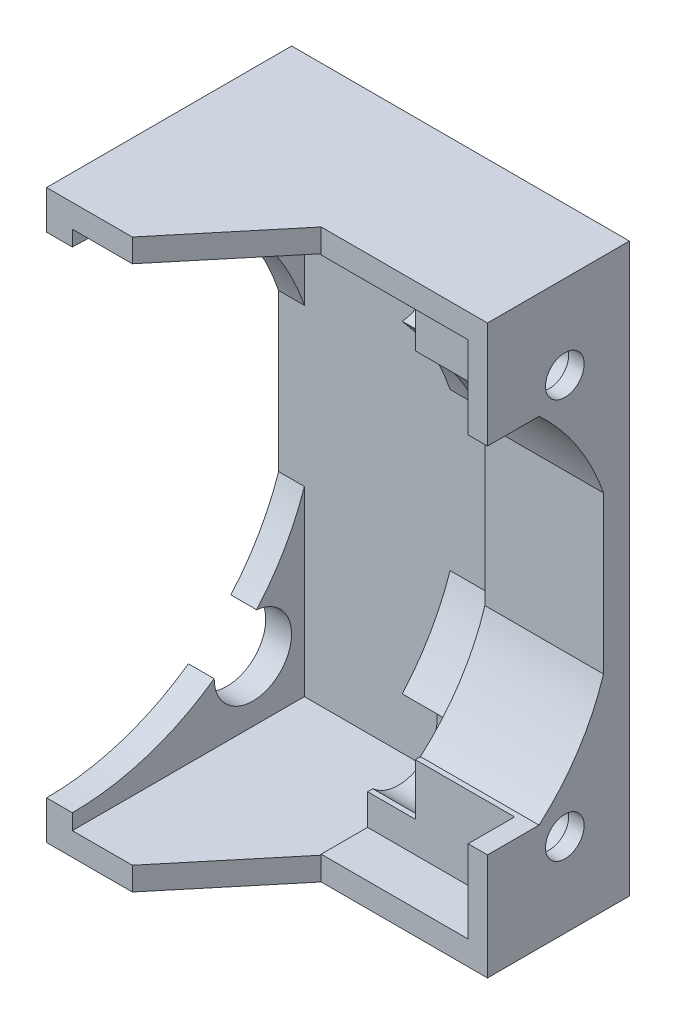
SolidWorks part; units mm, degrees
ref_plane "Alzado" through (0, 0, 0) normal (0, 0, 1) x (1, 0, 0)
ref_plane "Planta" through (0, 0, 0) normal (0, 1, 0) x (1, 0, 0)
ref_plane "Vista lateral" through (0, 0, 0) normal (1, 0, 0) x (0, 0, -1)
sketch "Croquis1" plane through (0, 0, 0) normal (0, 0, 1) x (1, 0, 0)
  line L1 (-34.6141, 8.9096) -> (-9.6141, 8.9096)
  line L2 (-34.6141, 8.9096) -> (-34.6141, -35.0904)
  line L3 (-34.6141, -35.0904) -> (-9.6141, -35.0904)
  line L4 (-9.6141, 8.9096) -> (-9.6141, -35.0904)
  dimension "D1" = 25
  dimension "D2" = 44
extrude "Saliente-Extruir1" add sketch "Croquis1" along normal blind 20
sketch "Croquis2" plane through (0, 0, 20) normal (0, 0, 1) x (1, 0, 0)
  line L0 (-34.6141, 8.9096) -> (-34.6141, -35.0904) construction
  line L1 (-32.6141, 7.1096) -> (-21.3141, 7.1096)
  line L2 (-32.6141, 7.1096) -> (-32.6141, -33.2904)
  line L3 (-32.6141, -33.2904) -> (-21.3141, -33.2904)
  line L4 (-21.3141, 7.1096) -> (-21.3141, -33.2904)
  line L5 (-9.6141, 8.9096) -> (-34.6141, 8.9096) construction
  dimension "D1" = 2
  dimension "D2" = 11.3
  dimension "D3" = 1.8
  dimension "D4" = 40.4
extrude "Cortar-Extruir1" cut sketch "Croquis2" against normal blind 18
sketch "Croquis3" plane through (0, 0, 20) normal (0, 0, 1) x (1, 0, 0)
  line L0 (-34.6141, -35.0904) -> (-9.6141, -35.0904) construction
  line L1 (-9.6141, 8.9096) -> (-20.3141, 8.9096)
  line L2 (-9.6141, 8.9096) -> (-9.6141, -35.0904)
  line L3 (-9.6141, -35.0904) -> (-20.3141, -35.0904)
  line L4 (-20.3141, 8.9096) -> (-20.3141, -35.0904)
  line L5 (-21.3141, -33.2904) -> (-21.3141, 7.1096) construction
  dimension "D1" = 1
extrude "Cortar-Extruir2" cut sketch "Croquis3" against normal blind 12
sketch "Croquis4" plane through (-34.6141, 0, 0) normal (-1, 0, 0) x (0, 0, 1)
  line L1 (20, 5.9096) -> (20, -32.0904)
  line L2 (0, 8.9096) -> (0, -35.0904) construction
  line L5 (20, 8.9096) -> (0, 8.9096) construction
  circle A0 centre (6, 2.4096) radius 1.6
  arc A1 (20, 5.9096) -> (20, -32.0904) centre (20, -13.0904) ccw
  circle A2 centre (6, -28.5904) radius 1.6
  dimension "D1" = 6
  dimension "D3" = 31
  dimension "D2" = 6.5
  dimension "D4" = 6
extrude "Cortar-Extruir3" cut sketch "Croquis4" against normal up to vertex
sketch "Croquis5" plane through (-34.6141, 0, 0) normal (-1, 0, 0) x (0, 0, 1)
  circle A0 centre (6, 2.4096) radius 3
  circle A1 centre (6, -28.5904) radius 3
extrude "Cortar-Extruir4" cut sketch "Croquis5" against normal blind 17
sketch "Croquis7" plane through (0, 0, 8) normal (0, 0, 1) x (1, 0, 0)
  line L0 (-20.3141, -30.8265) -> (-20.3141, -35.0904) construction
  line L1 (-9.6141, -35.0904) -> (-20.3141, -35.0904)
  line L2 (-9.6141, -35.0904) -> (-9.6141, -32.9585)
  line L3 (-9.6141, -32.9585) -> (-20.3141, -32.9585)
  line L4 (-20.3141, -35.0904) -> (-20.3141, -32.9585)
  line L5 (-20.3141, 8.9096) -> (-20.3141, 4.6456) construction
  line L6 (-9.6141, 8.9096) -> (-20.3141, 8.9096)
  line L7 (-9.6141, 8.9096) -> (-9.6141, 6.7776)
  line L8 (-9.6141, 6.7776) -> (-20.3141, 6.7776)
  line L9 (-20.3141, 8.9096) -> (-20.3141, 6.7776)
extrude "Saliente-Extruir2" add sketch "Croquis7" along normal up to vertex (12 mm away)
sketch "Croquis9" plane through (0, 0, 2) normal (0, 0, 1) x (1, 0, 0)
  line L1 (-21.3141, -7.0077) -> (-32.6141, -7.0077)
  line L2 (-21.3141, -7.0077) -> (-21.3141, -19.1732)
  line L3 (-21.3141, -19.1732) -> (-32.6141, -19.1732)
  line L4 (-32.6141, -7.0077) -> (-32.6141, -19.1732)
extrude "Saliente-Extruir3" add sketch "Croquis9" against normal up to vertex (2 mm away)
sketch "Croquis11" plane through (-32.6141, 0, 0) normal (-1, 0, 0) x (0, 0, 1)
  line L0 (2, -7.0077) -> (2, -19.1732)
  arc A0 (2, -7.0077) -> (2, -19.1732) centre (20, -13.0904) ccw
extrude "Saliente-Extruir4" add sketch "Croquis11" along normal up to vertex (2 mm away)
sketch "Croquis12" plane through (-34.6141, 0, 0) normal (-1, 0, 0) x (0, 0, 1)
  line L0 (20, -35.0904) -> (0, -35.0904) construction
  line L1 (0, 8.9096) -> (0.99, 8.9096)
  line L2 (0, 8.9096) -> (0, -35.0904)
  line L3 (0, -35.0904) -> (0.99, -35.0904)
  line L4 (0.99, 8.9096) -> (0.99, -35.0904)
  dimension "D1" = 0.99
extrude "Cortar-Extruir10" cut sketch "Croquis12" against normal up to vertex
sketch "Croquis13" plane through (-9.6141, 0, 0) normal (1, 0, 0) x (0, 0, -1)
  line L0 (-20, 8.9096) -> (-0.99, 8.9096) construction
  line L1 (-20, -35.0904) -> (-12, -35.0904)
  line L2 (-20, -35.0904) -> (-20, 8.9096)
  line L3 (-20, 8.9096) -> (-12, 8.9096)
  line L4 (-12, -35.0904) -> (-12, 8.9096)
  dimension "D1" = 8
extrude "Cortar-Extruir11" cut sketch "Croquis13" against normal up to vertex (11.7 mm away)
sketch "Croquis14" plane through (-21.3141, 0, 0) normal (1, 0, 0) x (0, 0, -1)
  line L0 (-2, -19.1732) -> (-2, -7.0077)
  arc A0 (-2, -19.1732) -> (-2, -7.0077) centre (-20, -13.0904) ccw
extrude "Saliente-Extruir5" add sketch "Croquis14" along normal up to vertex (11.7 mm away)
sketch "Croquis15" plane through (0, 0, 12) normal (0, 0, 1) x (1, 0, 0)
  line L1 (-9.6141, 6.7776) -> (-9.6141, 8.9096) construction
  line L2 (-20.3777, -33.4585) -> (-9.6141, -33.4585)
  line L3 (-20.3777, -33.4585) -> (-20.3777, 7.2776)
  line L4 (-20.3777, 7.2776) -> (-9.6141, 7.2776)
  line L8 (-9.6141, -33.4585) -> (-9.6141, 7.2776)
  line L9 (-20.3141, -32.9585) -> (-9.6141, -32.9585) construction
  line L10 (-9.6141, 6.7776) -> (-20.3141, 6.7776) construction
  dimension "D1" = 0.5
  dimension "D2" = 0.5
extrude "Cortar-Extruir12" cut sketch "Croquis15" against normal up to vertex (4 mm away)
sketch "Croquis16" plane through (-9.6141, 0, 0) normal (1, 0, 0) x (0, 0, -1)
  line L0 (-8, -27.8213) -> (-8, -33.4585)
  line L1 (-8, -33.4585) -> (-12, -33.4585)
  line L2 (-12, -33.4585) -> (-12, -35.0904)
  line L3 (-12, -35.0904) -> (-0.99, -35.0904)
  line L4 (-0.99, -35.0904) -> (-0.99, 8.9096)
  line L5 (-0.99, -35.0904) -> (-0.99, 8.9096) construction
  line L6 (-2, -7.0077) -> (-2, -19.1732)
  line L7 (-2, -7.0077) -> (-2, -19.1732) construction
  line L8 (-2, -13.0904) -> (-0.99, -13.0904) construction
  line L9 (-12, 8.9096) -> (-0.99, 8.9096)
  line L10 (-12, 7.2776) -> (-12, 8.9096)
  line L11 (-8, 7.2776) -> (-12, 7.2776)
  line L12 (-8, 1.6405) -> (-8, 7.2776)
  arc A0 (-8, -27.8213) -> (-2, -19.1732) centre (-20, -13.0904) ccw
  arc A1 (-8, 1.6405) -> (-2, -7.0077) centre (-20, -13.0904) cw
  circle A2 centre (-6, -28.5904) radius 1.5
  circle A3 centre (-6, 2.4096) radius 1.5
extrude "Saliente-Extruir6" add sketch "Croquis16" along normal blind 1.2
sketch "Croquis17" plane through (0, -35.0904, 0) normal (0, -1, 0) x (1, 0, 0)
  line L0 (-21.3141, 12) -> (-21.3141, 20)
  line L1 (-21.3141, 20) -> (-27.9641, 20)
  line L2 (-34.6141, 20) -> (-21.3141, 20) construction
  line L3 (-27.9641, 20) -> (-21.3141, 12)
extrude "Cortar-Extruir13" cut sketch "Croquis17" against normal up to vertex
sketch "Croquis18" plane through (0, 0, 12) normal (0, 0, 1) x (1, 0, 0)
  line L2 (-20.3777, 7.2776) -> (-21.3141, 7.2776)
  line L3 (-20.3777, 7.2776) -> (-20.3777, -33.2904)
  line L4 (-20.3777, -33.2904) -> (-21.3141, -33.2904)
  line L5 (-21.3141, 7.2776) -> (-21.3141, -33.2904)
extrude "Cortar-Extruir14" cut sketch "Croquis18" against normal up to vertex (4 mm away)
sketch "Croquis19" plane through (-8.4141, 0, 0) normal (1, 0, 0) x (0, 0, -1)
  line L0 (-2, -19.1732) -> (-2, -7.0077)
  line L1 (-8, -27.8213) -> (-8, -26.8213)
  line L2 (-8, 1.6405) -> (-8, 0.6405)
  line L3 (-3, -19.1732) -> (-3, -7.0077)
  arc A0 (-2, -19.1732) -> (-8, -27.8213) centre (-20, -13.0904) cw
  arc A1 (-2, -7.0077) -> (-8, 1.6405) centre (-20, -13.0904) ccw
  arc A2 (-8, -26.8213) -> (-3, -19.1732) centre (-19.1028, -14.1044) ccw
  arc A3 (-8, 0.6405) -> (-3, -7.0077) centre (-20.7177, -13.1322) cw
  dimension "D1" = 1
  dimension "D3" = 1
  dimension "D4" = 12.1655
  dimension "D5" = 1
extrude "Saliente-Extruir7" add sketch "Croquis19" against normal up to vertex
sketch "Croquis20" plane through (-8.4141, 0, 0) normal (1, 0, 0) x (0, 0, -1)
  line L1 (-8, -33.4585) -> (-12, -33.4585)
  line L2 (-8, -33.4585) -> (-8, -33.2224)
  line L3 (-8, -33.2224) -> (-12, -33.2224)
  line L4 (-12, -33.4585) -> (-12, -33.2224)
  line L5 (-8, 7.2776) -> (-12, 7.2776)
  line L6 (-8, 7.2776) -> (-8, 7.0276)
  line L7 (-8, 7.0276) -> (-12, 7.0276)
  line L8 (-12, 7.2776) -> (-12, 7.0276)
  dimension "D1" = 0.25
  dimension "D2" = 40.25
extrude "Saliente-Extruir8" add sketch "Croquis20" against normal up to vertex
sketch "Croquis21" plane through (-8.4141, 0, 0) normal (1, 0, 0) x (0, 0, -1)
  line L1 (-12, -33.2224) -> (-8, -33.2224)
  line L2 (-12, -33.2224) -> (-12, -26.8213)
  line L3 (-12, -26.8213) -> (-8, -26.8213)
  line L4 (-8, -33.2224) -> (-8, -26.8213)
  line L5 (-8, 0.6405) -> (-12, 0.6405)
  line L6 (-8, 0.6405) -> (-8, 7.0276)
  line L7 (-8, 7.0276) -> (-12, 7.0276)
  line L8 (-12, 0.6405) -> (-12, 7.0276)
extrude "Saliente-Extruir9" add sketch "Croquis21" against normal blind 1.5
sketch "Croquis22" plane through (0, 0, 8) normal (0, 0, 1) x (1, 0, 0)
  line L0 (-9.9141, 7.0276) -> (-21.3141, 7.0276)
  line L1 (-21.3141, 7.0276) -> (-21.3141, 4.6456)
  line L2 (-21.3141, 4.6456) -> (-17.6141, 4.6456)
  line L3 (-17.6141, 4.6456) -> (-17.6141, 0.6405)
  line L4 (-17.6141, 0.6405) -> (-9.9141, 0.6405)
  line L5 (-9.9141, 0.6405) -> (-9.9141, 7.0276)
  line L6 (-9.9141, -26.8213) -> (-17.6141, -26.8213)
  line L7 (-17.6141, -26.8213) -> (-17.6141, -30.8265)
  line L8 (-17.6141, -30.8265) -> (-21.3141, -30.8265)
  line L9 (-21.3141, -30.8265) -> (-21.3141, -33.2224)
  line L10 (-21.3141, -33.2224) -> (-9.9141, -33.2224)
  line L11 (-9.9141, -33.2224) -> (-9.9141, -26.8213)
extrude "Saliente-Extruir10" add sketch "Croquis22" along normal blind 0.4
